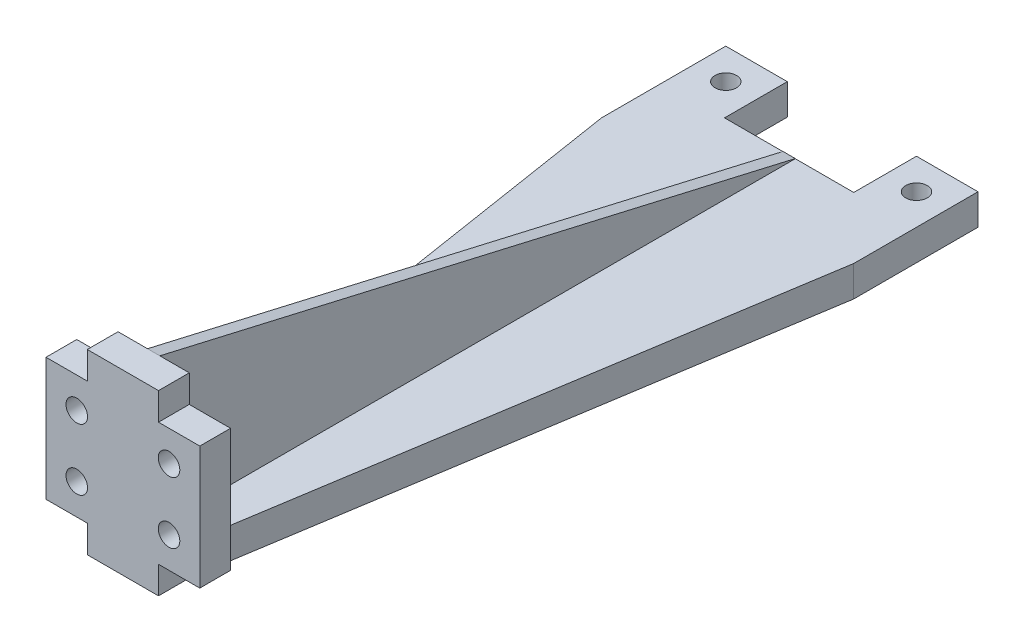
SolidWorks part; units mm, degrees
ref_plane "Front Plane" through (0, 0, 0) normal (0, 0, 1) x (1, 0, 0)
ref_plane "Top Plane" through (0, 0, 0) normal (0, 1, 0) x (1, 0, 0)
ref_plane "Right Plane" through (0, 0, 0) normal (1, 0, 0) x (0, 0, -1)
sketch "Sketch1" plane through (0, 0, 0) normal (0, 1, 0) x (1, 0, 0)
  line L1 (0, 0) -> (41, 0)
  line L2 (0, 0) -> (0, 118.5)
  line L3 (0, 118.5) -> (41, 118.5)
  line L4 (41, 0) -> (41, 118.5)
  dimension "D1" = 41
  dimension "D2" = 118.5
extrude "Boss-Extrude1" add sketch "Sketch1" along normal blind 5
sketch "Sketch2" plane through (0, 5, 0) normal (0, 1, 0) x (1, 0, 0)
  line L1 (0, 118.5) -> (10, 118.5) construction
  line L2 (0, 118.5) -> (0, 108.3) construction
  line L3 (0, 108.3) -> (10, 108.3) construction
  line L4 (10, 118.5) -> (10, 108.3) construction
  line L5 (41, 118.5) -> (31, 118.5) construction
  line L6 (41, 118.5) -> (41, 108.3) construction
  line L7 (41, 108.3) -> (31, 108.3) construction
  line L8 (31, 118.5) -> (31, 108.3) construction
  line L9 (10, 118.5) -> (31, 118.5)
  line L10 (10, 118.5) -> (10, 108.3)
  line L11 (10, 108.3) -> (31, 108.3)
  line L12 (31, 118.5) -> (31, 108.3)
  dimension "D1" = 10.2
  dimension "D3" = 10
  dimension "D4" = 10
extrude "Cut-Extrude1" cut sketch "Sketch2" against normal through all
sketch "Sketch9" plane through (0, 5, 0) normal (0, 1, 0) x (1, 0, 0)
  line L1 (0, 118.5) -> (5, 118.5) construction
  line L2 (0, 118.5) -> (0, 113.5) construction
  line L3 (0, 113.5) -> (5, 113.5) construction
  line L4 (5, 118.5) -> (5, 113.5) construction
  line L5 (31, 118.5) -> (36, 118.5) construction
  line L6 (31, 118.5) -> (31, 113.5) construction
  line L7 (31, 113.5) -> (36, 113.5) construction
  line L8 (36, 118.5) -> (36, 113.5) construction
  circle A0 centre (5, 113.5) radius 1.75
  circle A1 centre (36, 113.5) radius 1.75
  dimension "D3" = 3.5
  dimension "D4" = 3.5
  dimension "D1" = 5
  dimension "D2" = 5
extrude "Cut-Extrude4" cut sketch "Sketch9" against normal through all
sketch "Sketch11" plane through (0, 5, 0) normal (0, 1, 0) x (1, 0, 0)
  line L0 (20.5, 108.3) -> (20.5, 0) construction
  line L1 (10, 108.3) -> (31, 108.3) construction
  line L2 (0, 0) -> (41, 0) construction
  line L3 (15.5, 0) -> (25.5, 0) construction
  line L4 (15.5, 0) -> (0, 98.3)
  line L5 (0, 118.5) -> (0, 0) construction
  line L6 (25.5, 0) -> (41, 98.3)
  line L7 (41, 0) -> (41, 118.5) construction
  line L8 (0, 98.3) -> (0, 0)
  line L9 (0, 0) -> (15.5, 0)
  line L10 (41, 98.3) -> (41, 0)
  line L11 (41, 0) -> (25.5, 0)
  point P8 (20.5, 0)
  dimension "D1" = 10
  dimension "D2" = 10
extrude "Cut-Extrude5" cut sketch "Sketch11" against normal through all
sketch "Slider Reference" plane through (0, 0, 0) normal (0, 0, 1) x (1, 0, 0)
  line L0 (15.5, 0) -> (25.5, 0) construction
  line L1 (8, 0) -> (33, 0) construction
  line L2 (8, 0) -> (8, 28.9) construction
  line L3 (8, 28.9) -> (33, 28.9) construction
  line L4 (33, 0) -> (33, 28.9) construction
  line L6 (13, 19.45) -> (28, 19.45) construction
  line L7 (13, 19.45) -> (13, 9.45) construction
  line L8 (13, 9.45) -> (28, 9.45) construction
  line L9 (28, 19.45) -> (28, 9.45) construction
  line L10 (8, 24.45) -> (33, 24.45) construction
  line L11 (8, 24.45) -> (8, 4.45) construction
  line L12 (8, 4.45) -> (33, 4.45) construction
  line L13 (33, 24.45) -> (33, 4.45) construction
  point P5 (20.5, 0)
  point P8 (20.5, 0)
  point P13 (13, 14.45)
  point P14 (8, 14.45)
  point P15 (20.5, 19.45)
  point P16 (20.5, 28.9)
  dimension "D1" = 28.9
  dimension "D2" = 25
  dimension "D3" = 10
  dimension "D4" = 15
  dimension "D5" = 5
  dimension "D6" = 5
sketch "Sketch12" plane through (0, 5, 0) normal (0, 1, 0) x (1, 0, 0)
  line L0 (25.5, 0) -> (15.5, 0)
  line L1 (15.5, 0) -> (14.7116, 5)
  line L2 (15.5, 0) -> (0, 98.3) construction
  line L3 (14.7116, 5) -> (26.2884, 5)
  line L4 (41, 98.3) -> (25.5, 0) construction
  line L5 (26.2884, 5) -> (25.5, 0)
  dimension "D1" = 5
extrude "Boss-Extrude4" add sketch "Sketch12" along normal up to vertex (23.9 mm away) up to point (8, 28.9, 0)
sketch "Sketch16" plane through (0, 5, 0) normal (0, 1, 0) x (1, 0, 0)
  line L0 (10, 108.3) -> (31, 108.3) construction
  line L1 (19.5, 108.3) -> (21.5, 108.3)
  line L2 (19.5, 108.3) -> (19.5, 5)
  line L3 (19.5, 5) -> (21.5, 5)
  line L4 (21.5, 108.3) -> (21.5, 5)
  line L5 (26.2884, 5) -> (14.7116, 5) construction
  point P6 (20.5, 108.3)
  point P7 (20.5, 108.3)
  dimension "D1" = 2
extrude "Boss-Extrude5" add sketch "Sketch16" along normal up to surface (23.9 mm away) up to face at (20.5, 28.9, -2.5)
sketch "Sketch17" plane through (19.5, 0, 0) normal (-1, 0, 0) x (0, 0, 1)
  line L0 (-108.4, 5) -> (-5, 28.9)
  line L1 (-118.5, 5) -> (-98.3, 5) construction
  line L2 (-5, 28.9) -> (-108.3, 28.9)
  line L3 (-108.3, 28.9) -> (-108.4, 5)
  line L4 (-108.3, 28.9) -> (-108.3, 5) construction
extrude "Cut-Extrude8" cut sketch "Sketch17" against normal through all
sketch "Sketch23" plane through (0, 28.9, 0) normal (0, 1, 0) x (1, 0, 0)
  line L0 (26.2884, 5) -> (33, 5)
  line L1 (33, 5) -> (33, 0)
  line L2 (8, 0) -> (33, 0) construction
  line L3 (33, 0) -> (25.5, 0)
  line L4 (25.5, 0) -> (26.2884, 5)
  line L5 (14.7116, 5) -> (8, 5)
  line L6 (8, 5) -> (8, 0)
  line L7 (8, 0) -> (33, 0) construction
  line L8 (8, 0) -> (15.5, 0)
  line L9 (15.5, 0) -> (14.7116, 5)
extrude "Boss-Extrude6" add sketch "Sketch23" against normal up to surface (28.9 mm away) up to face at (20.5, 0, -88.72)
sketch "Sketch25" plane through (0, 0, -5) normal (0, 0, -1) x (-1, 0, 0)
  line L0 (-8, 4.45) -> (-33, 4.45) construction
  line L1 (-8, 4.45) -> (-14.7116, 4.45)
  line L3 (-8, 4.45) -> (-8, 0)
  line L4 (-8, 0) -> (-14.7116, 0)
  line L6 (-14.7116, 4.45) -> (-14.7116, 0)
  line L8 (-26.2884, 0) -> (-33, 0)
  line L9 (-26.2884, 0) -> (-26.2884, 4.45)
  line L10 (-26.2884, 4.45) -> (-33, 4.45)
  line L11 (-33, 0) -> (-33, 4.45)
  line L12 (-8, 24.45) -> (-33, 24.45) construction
  line L13 (-8, 28.9) -> (-14.7116, 28.9)
  line L14 (-8, 28.9) -> (-8, 24.45)
  line L15 (-8, 24.45) -> (-14.7116, 24.45)
  line L16 (-14.7116, 28.9) -> (-14.7116, 24.45)
  line L18 (-33, 28.9) -> (-26.2884, 28.9)
  line L19 (-33, 28.9) -> (-33, 24.45)
  line L20 (-33, 24.45) -> (-26.2884, 24.45)
  line L21 (-26.2884, 28.9) -> (-26.2884, 24.45)
extrude "Cut-Extrude9" cut sketch "Sketch25" against normal through all
sketch "Sketch26" plane through (0, 0, 0) normal (0, 0, 1) x (1, 0, 0)
  circle A0 centre (13, 19.45) radius 1.75
  circle A1 centre (28, 19.45) radius 1.75
  circle A2 centre (13, 9.45) radius 1.75
  circle A3 centre (28, 9.45) radius 1.75
  dimension "D1" = 3.5
extrude "Cut-Extrude10" cut sketch "Sketch26" against normal through all
